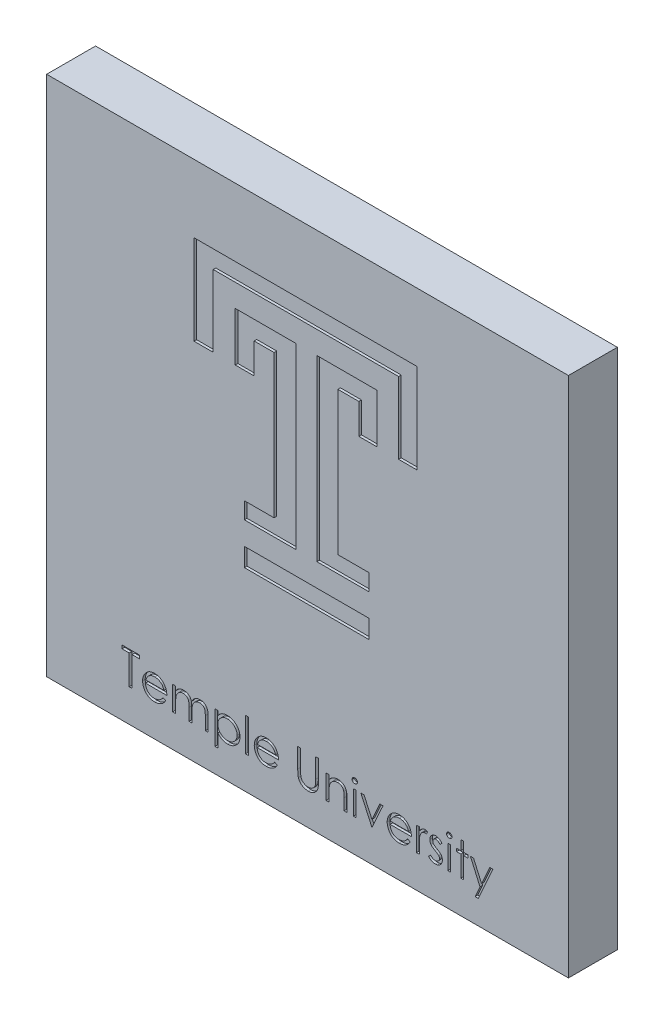
SolidWorks part; units mm, degrees
ref_plane "Front Plane" through (0, 0, 0) normal (0, 0, 1) x (1, 0, 0)
ref_plane "Top Plane" through (0, 0, 0) normal (0, 1, 0) x (1, 0, 0)
ref_plane "Right Plane" through (0, 0, 0) normal (1, 0, 0) x (0, 0, -1)
sketch "Sketch1" plane through (0, 0, 0) normal (0, 0, 1) x (1, 0, 0)
  line L1 (0, 0) -> (50.8, 0)
  line L2 (0, 0) -> (0, 50.8)
  line L3 (0, 50.8) -> (50.8, 50.8)
  line L4 (50.8, 0) -> (50.8, 50.8)
  dimension "D1" = 50.8
extrude "Boss-Extrude1" add sketch "Sketch1" along normal blind 4.7625
sketch "Sketch2" plane through (0, 0, 4.7625) normal (0, 0, 1) x (1, 0, 0)
  line L0 (73.421, 206.9679) -> (339.421, 206.9679) construction
  line L1 (25.4, 0) -> (25.4, 3.175) construction
  line L2 (0, 0) -> (50.8, 0) construction
  line L3 (6.35, 3.175) -> (44.45, 3.175) construction
  text T0 "Temple University"
  point P9 (25.4, 3.175)
  dimension "D1" = 38.1
  dimension "D2" = 3.175
extrude "Cut-Extrude1" cut sketch "Sketch2" against normal blind 0.254
sketch "Sketch4" plane through (0, 0, 4.7625) normal (0, 0, 1) x (1, 0, 0)
  line L0 (14.3425, 44.1908) -> (36.0746, 44.1908)
  line L1 (36.0746, 44.1908) -> (36.0746, 35.4645)
  line L2 (36.0746, 35.4645) -> (34.2636, 35.4645)
  line L3 (34.2636, 35.4645) -> (34.2636, 42.4455)
  line L4 (34.2636, 42.4455) -> (16.2194, 42.4455)
  line L5 (16.2194, 42.4455) -> (16.2194, 35.4645)
  line L6 (16.2194, 35.4645) -> (14.3425, 35.4645)
  line L7 (14.3425, 35.4645) -> (14.3425, 44.1908)
  line L8 (18.3597, 35.4645) -> (18.3597, 40.2392)
  line L9 (18.3597, 40.2392) -> (24.2866, 40.2392)
  line L10 (24.2866, 40.2392) -> (24.2866, 22.8565)
  line L11 (24.2866, 22.8565) -> (19.2474, 22.8565)
  line L12 (19.2474, 22.8565) -> (19.2474, 24.4687)
  line L13 (19.2474, 24.4687) -> (22.1397, 24.4687)
  line L14 (22.1397, 24.4687) -> (22.1397, 38.4097)
  line L15 (22.1397, 38.4097) -> (20.1957, 38.4097)
  line L16 (20.1957, 38.4097) -> (20.1957, 35.4645)
  line L17 (20.1957, 35.4645) -> (18.3597, 35.4645)
  line L18 (32.1444, 35.4645) -> (32.1444, 40.2392)
  line L19 (32.1444, 40.2392) -> (26.3123, 40.2392)
  line L20 (26.3123, 40.2392) -> (26.3123, 22.8565)
  line L21 (26.3123, 22.8565) -> (31.3857, 22.8565)
  line L22 (31.3857, 22.8565) -> (31.3857, 24.4687)
  line L23 (31.3857, 24.4687) -> (28.3512, 24.4687)
  line L24 (28.3512, 24.4687) -> (28.3512, 38.4097)
  line L25 (28.3512, 38.4097) -> (30.39, 38.4097)
  line L26 (30.39, 38.4097) -> (30.39, 35.4645)
  line L27 (30.39, 35.4645) -> (32.1444, 35.4645)
  line L28 (31.3857, 20.6229) -> (31.3857, 18.827)
  line L29 (31.3857, 18.827) -> (19.2474, 18.827)
  line L30 (19.2474, 18.827) -> (19.2474, 20.6229)
  line L31 (19.2474, 20.6229) -> (31.3857, 20.6229)
extrude "Cut-Extrude2" cut sketch "Sketch4" against normal blind 0.254 contours L14 L15 L16 L17 L8 L9 L10 L11 L12 L13
